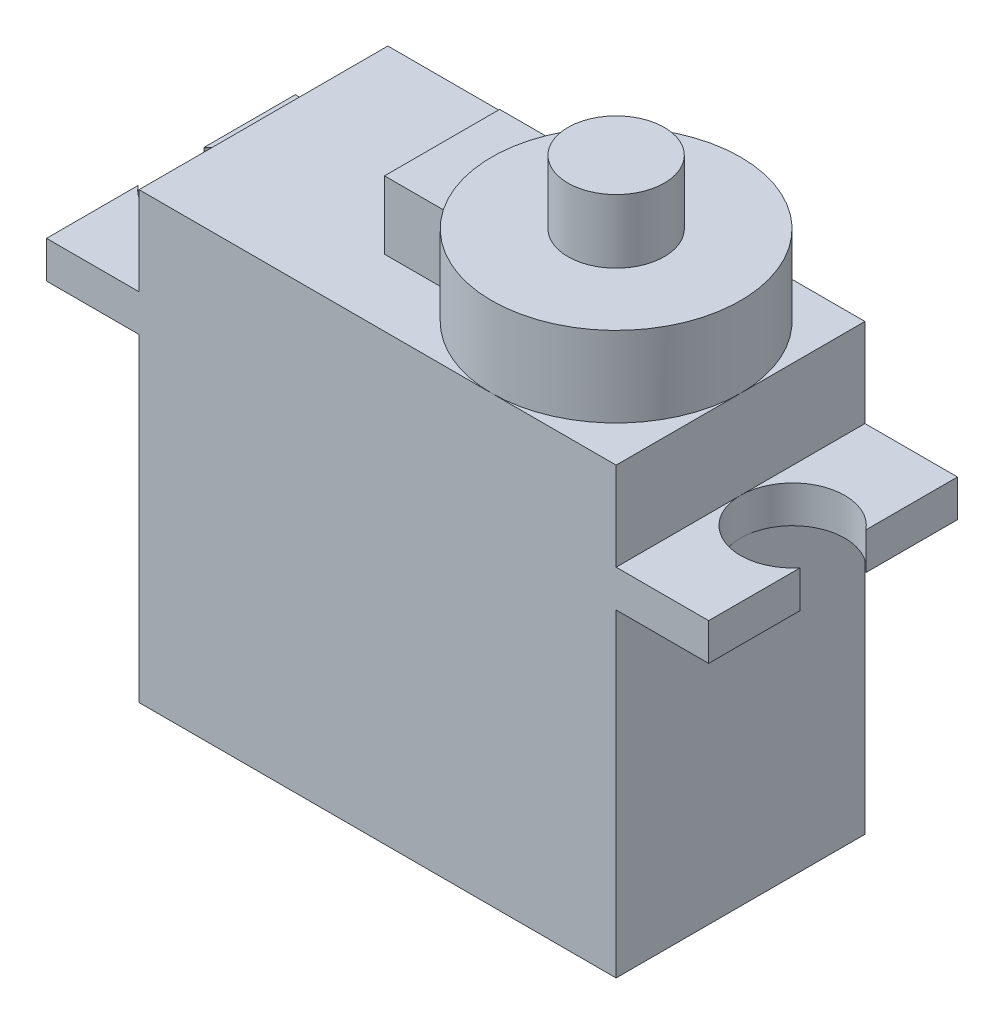
SolidWorks part; units mm, degrees
ref_plane "Front Plane" through (0, 0, 0) normal (0, 0, 1) x (1, 0, 0)
ref_plane "Top Plane" through (0, 0, 0) normal (0, 1, 0) x (1, 0, 0)
ref_plane "Right Plane" through (0, 0, 0) normal (1, 0, 0) x (0, 0, -1)
sketch "Sketch1" plane through (0, 0, 0) normal (0, 1, 0) x (1, 0, 0)
  line L1 (-11.6, 6.05) -> (11.6, 6.05)
  line L2 (-11.6, 6.05) -> (-11.6, -6.05)
  line L3 (-11.6, -6.05) -> (11.6, -6.05)
  line L4 (11.6, 6.05) -> (11.6, -6.05)
  line L5 (-11.6, 6.05) -> (11.6, -6.05) construction
  line L6 (-11.6, -6.05) -> (11.6, 6.05) construction
  point P0 (0, 0)
  dimension "D1" = 23.2
  dimension "D2" = 12.1
extrude "Boss-Extrude1" add sketch "Sketch1" along normal blind 21.6
sketch "Sketch2" plane through (-11.6, 0, 0) normal (-1, 0, 0) x (0, 0, 1)
  line L0 (-6.05, 21.6) -> (-6.05, 0) construction
  point P0 (-6.05, 15.5)
  dimension "D1" = 15.5
ref_plane "Plane1" through (0, 15.5, 0) normal (0, -1, 0) x (-1, 0, 0)
sketch "Sketch3" plane through (0, 15.5, 0) normal (0, -1, 0) x (-1, 0, 0)
  line L0 (0, 6.05) -> (0, -6.05) construction
  line L1 (-11.6, 6.05) -> (-16.1, 6.05)
  line L2 (-11.6, 6.05) -> (-11.6, -6.05)
  line L3 (-11.6, -6.05) -> (-16.1, -6.05)
  line L4 (-16.1, 6.05) -> (-16.1, 1.6)
  line L5 (-11.6, 6.05) -> (11.6, 6.05) construction
  line L6 (11.6, -6.05) -> (-11.6, -6.05) construction
  line L7 (16.1, 6.05) -> (16.1, 1.6)
  line L8 (11.6, -6.05) -> (16.1, -6.05)
  line L9 (11.6, 6.05) -> (11.6, -6.05)
  line L10 (11.6, 6.05) -> (16.1, 6.05)
  line L11 (-16.1, -1.6) -> (-16.1, -6.05)
  line L12 (16.1, -1.6) -> (16.1, -6.05)
  arc A0 (-16.1, -1.6) -> (-16.1, 1.6) centre (-14.1344, 0) ccw
  arc A1 (16.1, -1.6) -> (16.1, 1.6) centre (14.1344, 0) cw
  point P7 (-11.6, 0)
  point P8 (-16.1, 1.6)
  point P9 (-16.1, -1.6)
  point P24 (11.6, 0)
  dimension "D1" = 4.5
  dimension "D2" = 4.45
  dimension "D3" = 4.45
extrude "Boss-Extrude2" add sketch "Sketch3" against normal blind 1.8 contours A0 L2 L1 L4 | A0 L11 L3 L2 | L12 A1 L9 L8 | L9 A1 L7 L10
sketch "Sketch5" plane through (0, 21.6, 0) normal (0, 1, 0) x (1, 0, 0)
  line L0 (11.6, -6.05) -> (11.6, 6.05) construction
  circle A0 centre (5.55, 0) radius 6.05
  point P0 (5.55, 0)
  dimension "D2" = 12.1
  dimension "D1" = 6.05
extrude "Boss-Extrude3" add sketch "Sketch5" along normal blind 3.9
sketch "Sketch6" plane through (0, 25.5, 0) normal (0, 1, 0) x (1, 0, 0)
  circle A0 centre (5.55, 0) radius 2.345
  point P0 (5.55, 0)
  dimension "D1" = 4.69
extrude "Boss-Extrude4" add sketch "Sketch6" along normal blind 3.1
sketch "Sketch7" plane through (0, 21.6, 0) normal (0, 1, 0) x (1, 0, 0)
  line L1 (-2.9131, 2.8) -> (1.0131, 2.8)
  line L2 (-2.9131, 2.8) -> (-2.9131, -2.8)
  line L3 (-2.9131, -2.8) -> (1.0131, -2.8)
  line L4 (1.0131, 2.8) -> (1.0131, -2.8)
  line L5 (-2.9131, 2.8) -> (1.0131, -2.8) construction
  line L6 (-2.9131, -2.8) -> (1.0131, 2.8) construction
  circle A0 centre (5.55, 0) radius 6.05 construction
  point P0 (-0.95, 0)
  point P1 (5.55, 0)
  point P2 (-0.95, 0)
  point P8 (0.1869, 2.8)
  dimension "D1" = 6.5
  dimension "D2" = 5.6
  dimension "D3" = 3.1
extrude "Boss-Extrude5" add sketch "Sketch7" along normal blind 3.3
